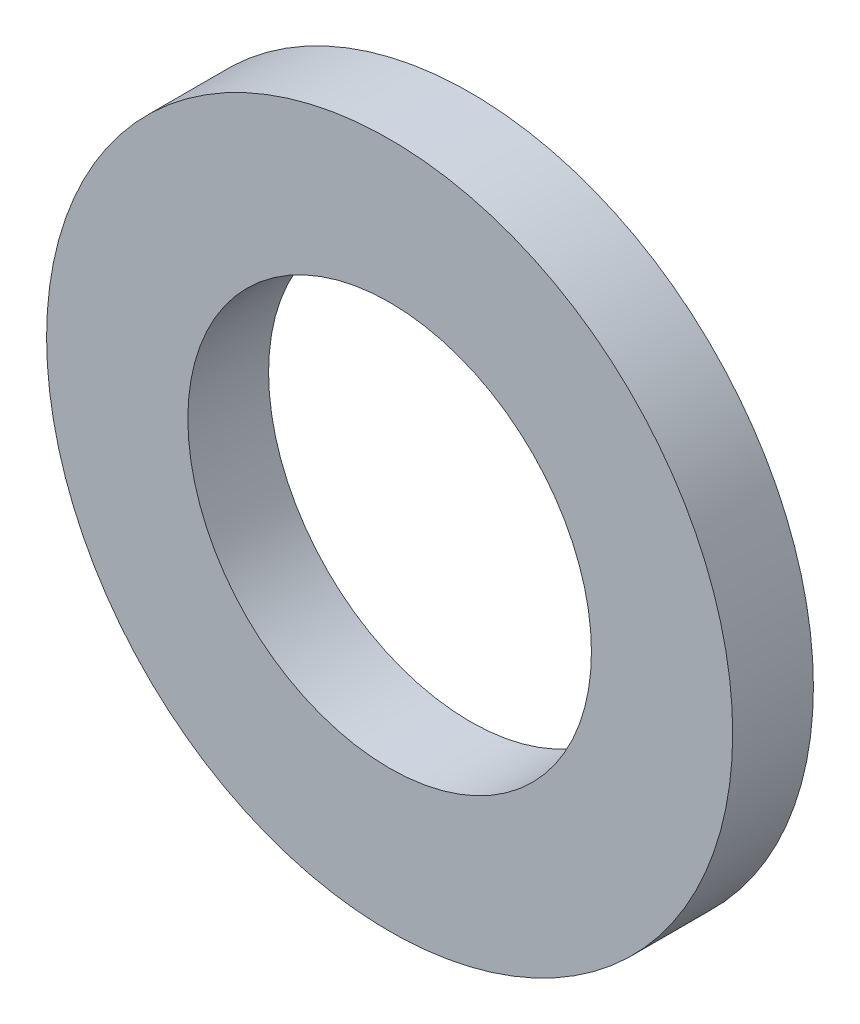
SolidWorks part; units mm, degrees
ref_plane "Plan de face" through (0, 0, 0) normal (0, 0, 1) x (1, 0, 0)
ref_plane "Plan de dessus" through (0, 0, 0) normal (0, 1, 0) x (1, 0, 0)
ref_plane "Plan de droite" through (0, 0, 0) normal (1, 0, 0) x (0, 0, -1)
sketch "Esquisse1" plane through (0, 0, 0) normal (0, 0, 1) x (1, 0, 0)
  circle A0 centre (0, 0) radius 2.5
  circle A1 centre (0, 0) radius 4.25
  dimension "D1" = 5
  dimension "D2" = 8.5
extrude "Extrusion1" add sketch "Esquisse1" along normal blind 1
